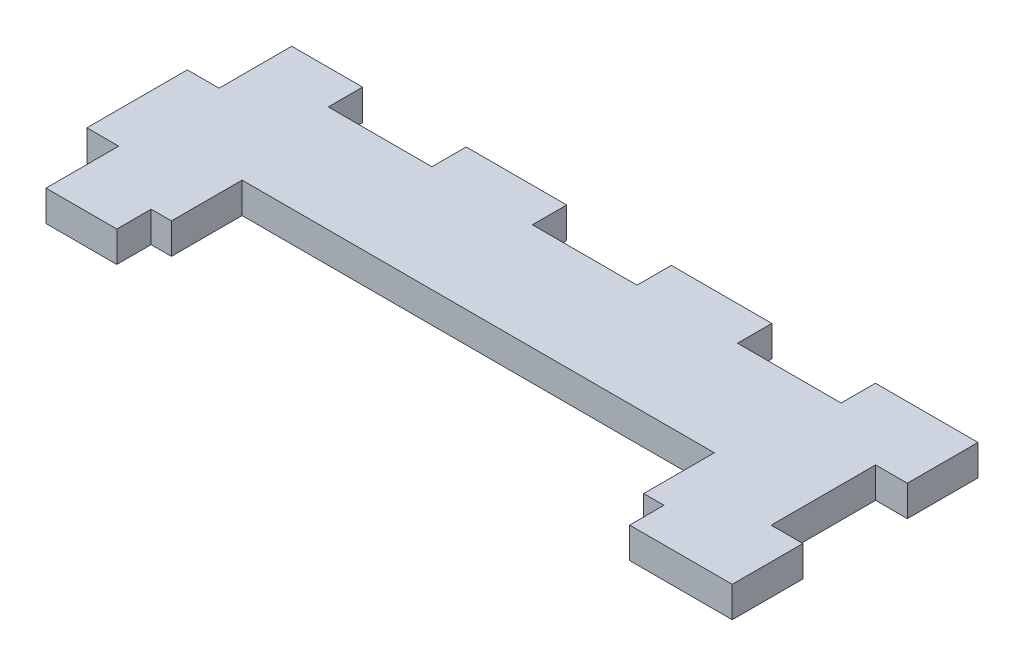
SolidWorks part; units mm, degrees
ref_plane "Front Plane" through (0, 0, 0) normal (0, 0, 1) x (1, 0, 0)
ref_plane "Top Plane" through (0, 0, 0) normal (0, 1, 0) x (1, 0, 0)
ref_plane "Right Plane" through (0, 0, 0) normal (1, 0, 0) x (0, 0, -1)
sketch "Sketch1" plane through (0, 0, 0) normal (0, 1, 0) x (1, 0, 0)
  line L0 (-32.0585, 21.25) -> (35.0585, 21.25) construction
  line L1 (-32.0585, 0) -> (35.0585, 0) construction
  line L2 (-32.0585, 0) -> (-32.0585, 25) construction
  line L3 (-32.0585, 25) -> (35.0585, 25) construction
  line L4 (35.0585, 0) -> (35.0585, 25) construction
  line L5 (0, 0) -> (0, 25) construction
  line L6 (35.0585, 3.75) -> (-32.0585, 3.75) construction
  line L7 (-32.0585, 10.75) -> (35.0585, 10.75) construction
  line L8 (-24.9418, 0) -> (-24.9418, 3.75)
  line L9 (-24.9418, 3.75) -> (-23.0585, 3.75)
  line L10 (-23.0585, 3.75) -> (-23.0585, 10.75)
  line L11 (-23.0585, 10.75) -> (23.0585, 10.75)
  line L12 (23.0585, 10.75) -> (23.0585, 3.75)
  line L13 (23.0585, 3.75) -> (24.9418, 3.75)
  line L14 (24.9418, 3.75) -> (24.9418, 0)
  line L15 (24.9418, 0) -> (35.0585, 0)
  line L16 (-24.9418, 0) -> (-32.0585, 0)
  line L17 (-24.9418, 25) -> (-24.9418, 21.25)
  line L18 (-24.9418, 21.25) -> (-15.0251, 21.25)
  line L19 (-15.0251, 21.25) -> (-15.0251, 25)
  line L20 (-15.0251, 25) -> (-5.0084, 25)
  line L21 (-5.0084, 25) -> (-5.0084, 21.25)
  line L22 (-5.0084, 21.25) -> (5.0084, 21.25)
  line L23 (5.0084, 21.25) -> (5.0084, 25)
  line L24 (-24.9418, 25) -> (-32.0585, 25)
  line L25 (-32.0585, 25) -> (-32.0585, 17.5)
  line L26 (-32.0585, 17.5) -> (-35.0585, 17.5)
  line L27 (-35.0585, 17.5) -> (-35.0585, 7.5)
  line L28 (-32.0585, 12.5) -> (0, 12.5) construction
  line L29 (-35.0585, 7.5) -> (-32.0585, 7.5)
  line L30 (-32.0585, 0) -> (-32.0585, 7.5)
  line L31 (35.0585, 17.5) -> (32.0585, 17.5)
  line L32 (32.0585, 17.5) -> (32.0585, 7.5)
  line L33 (32.0585, 7.5) -> (35.0585, 7.5)
  line L34 (35.0585, 7.5) -> (35.0585, 0)
  line L35 (35.0585, 17.5) -> (35.0585, 25)
  line L36 (5.0084, 25) -> (15.0251, 25)
  line L37 (15.0251, 25) -> (15.0251, 21.25)
  line L38 (15.0251, 21.25) -> (24.9418, 21.25)
  line L39 (24.9418, 21.25) -> (24.9418, 25)
  line L40 (24.9418, 25) -> (35.0585, 25)
  dimension "D1" = 7
  dimension "D2" = 10
sketch "Sketch3" plane through (0, 0, 0) normal (0, 1, 0) x (1, 0, 0)
  line L0 (-35.0585, 17.4) -> (-35.0585, 7.6)
  line L1 (-35.0585, 7.6) -> (-31.9585, 7.6)
  line L2 (-31.9585, 7.6) -> (-31.9585, 0.5)
  line L3 (-31.9585, 0.5) -> (-25.0418, 0.5)
  line L4 (-25.0418, 0.5) -> (-25.0418, 3.85)
  line L5 (-25.0418, 3.85) -> (-23.0585, 3.85)
  line L6 (-23.0585, 3.75) -> (-23.0585, 10.75) construction
  line L7 (-23.0585, 3.85) -> (-23.0585, 10.75)
  line L8 (-23.0585, 10.75) -> (23.0585, 10.75)
  line L9 (-35.0585, 17.4) -> (-31.9585, 17.4)
  line L10 (-31.9585, 17.4) -> (-31.9585, 24.5)
  line L11 (-31.9585, 24.5) -> (-25.0418, 24.5)
  line L12 (-25.0418, 24.5) -> (-25.0418, 21.15)
  line L13 (-25.0418, 21.15) -> (-14.9251, 21.15)
  line L14 (-14.9251, 21.15) -> (-14.9251, 24.5)
  line L15 (-14.9251, 24.5) -> (-5.1084, 24.5)
  line L16 (-5.1084, 24.5) -> (-5.1084, 21.15)
  line L17 (-5.1084, 21.15) -> (5.1084, 21.15)
  line L18 (5.1084, 21.15) -> (5.1084, 24.5)
  line L19 (5.1084, 24.5) -> (14.9251, 24.5)
  line L20 (14.9251, 24.5) -> (14.9251, 21.15)
  line L21 (14.9251, 21.15) -> (25.0418, 21.15)
  line L22 (25.0418, 21.15) -> (25.0418, 24.5)
  line L23 (25.0418, 24.5) -> (35.0585, 24.5)
  line L24 (35.0585, 24.5) -> (35.0585, 17.6)
  line L25 (35.0585, 17.6) -> (31.9585, 17.6)
  line L26 (31.9585, 17.6) -> (31.9585, 7.4)
  line L27 (31.9585, 7.4) -> (35.0585, 7.4)
  line L28 (35.0585, 7.5) -> (35.0585, 0) construction
  line L29 (35.0585, 7.4) -> (35.0585, 0.5)
  line L30 (35.0585, 0.5) -> (25.0418, 0.5)
  line L31 (25.0418, 0.5) -> (25.0418, 3.85)
  line L32 (25.0418, 3.85) -> (23.0585, 3.85)
  line L33 (23.0585, 10.75) -> (23.0585, 3.75) construction
  line L34 (23.0585, 3.85) -> (23.0585, 10.75)
  line L35 (35.0585, 17.5) -> (35.0585, 25) construction
  line L36 (-32.0585, 12.5) -> (0, 12.5) construction
  line L37 (-24.9418, 25) -> (-32.0585, 25) construction
  line L38 (-35.0585, 17.5) -> (-35.0585, 7.5) construction
  line L39 (-32.0585, 17.5) -> (-32.0585, 17.4) construction
  line L40 (-32.0585, 0) -> (-32.0585, 25) construction
  line L41 (-32.0585, 17.5) -> (-31.9585, 17.5) construction
  line L42 (-24.9418, 21.25) -> (-24.9418, 21.15) construction
  line L43 (-24.9418, 21.25) -> (-25.0418, 21.25) construction
  line L44 (-32.0585, 21.25) -> (35.0585, 21.25) construction
  line L45 (-15.0251, 21.25) -> (-14.9251, 21.25) construction
  line L46 (5.0084, 21.25) -> (5.1084, 21.25) construction
  line L47 (15.0251, 21.25) -> (14.9251, 21.25) construction
  line L48 (24.9418, 21.25) -> (25.0418, 21.25) construction
  line L49 (32.0585, 17.5) -> (32.0585, 17.6) construction
  line L50 (32.0585, 17.5) -> (31.9585, 17.5) construction
  line L51 (32.0585, 7.5) -> (32.0585, 7.4) construction
  line L52 (24.9418, 3.75) -> (25.0418, 3.75) construction
  line L53 (35.0585, 3.75) -> (-32.0585, 3.75) construction
  line L54 (24.9418, 3.75) -> (24.9418, 3.85) construction
  line L55 (-24.9418, 3.75) -> (-24.9418, 3.85) construction
  line L56 (-24.9418, 3.75) -> (-25.0418, 3.75) construction
  line L57 (-5.0084, 21.25) -> (-5.1084, 21.25) construction
  line L58 (-32.0585, 25) -> (-32.0585, 17.5) construction
  line L59 (-32.0585, 7.5) -> (-32.0585, 7.6) construction
  dimension "D1" = 0.5
  dimension "D2" = 0.1
sketch "Sketch4" plane through (0, 0, 0) normal (1, 0, 0) x (0, 0, -1)
  line L1 (21.15, 0) -> (10.75, 0)
  line L2 (21.15, 0) -> (21.15, -3)
  line L3 (21.15, -3) -> (10.75, -3)
  line L4 (10.75, 0) -> (10.75, -3)
extrude "Boss-Extrude1" add sketch "Sketch3" against normal up to vertex (3 mm away) up to point (0, -3, -21.15)
